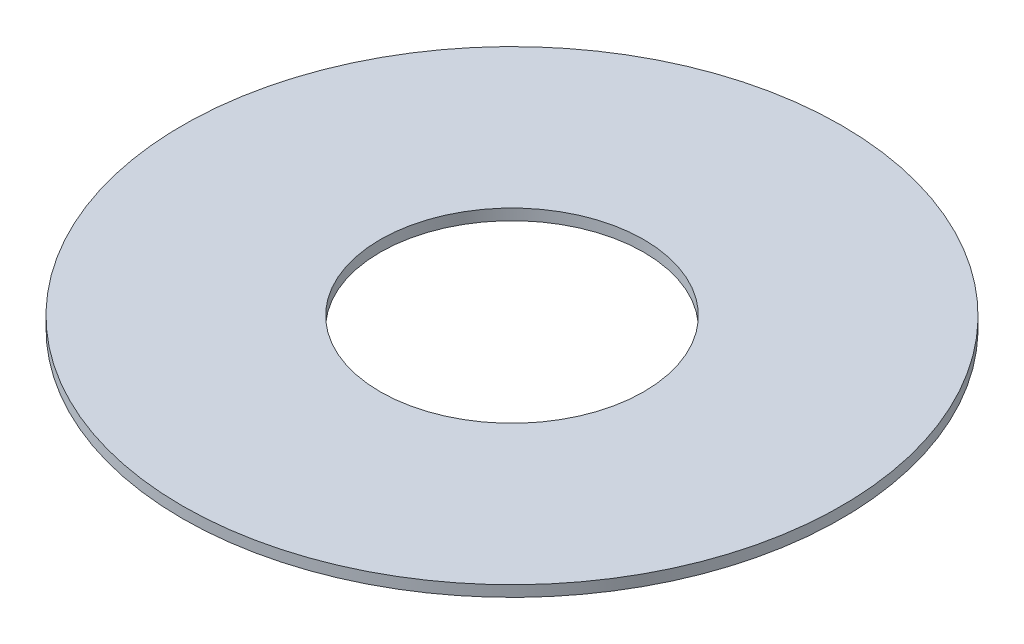
SolidWorks part; units mm, degrees
ref_plane "Front Plane" through (0, 0, 0) normal (0, 0, 1) x (1, 0, 0)
ref_plane "Top Plane" through (0, 0, 0) normal (0, 1, 0) x (1, 0, 0)
ref_plane "Right Plane" through (0, 0, 0) normal (1, 0, 0) x (0, 0, -1)
sketch "Sketch1" plane through (0, 0, 0) normal (0, 1, 0) x (1, 0, 0)
  circle A0 centre (0, 0) radius 1.2
  circle A1 centre (0, 0) radius 3
  dimension "D1" = 2.4
  dimension "D2" = 6
extrude "Extrude1" add sketch "Sketch1" along normal blind 0.1
